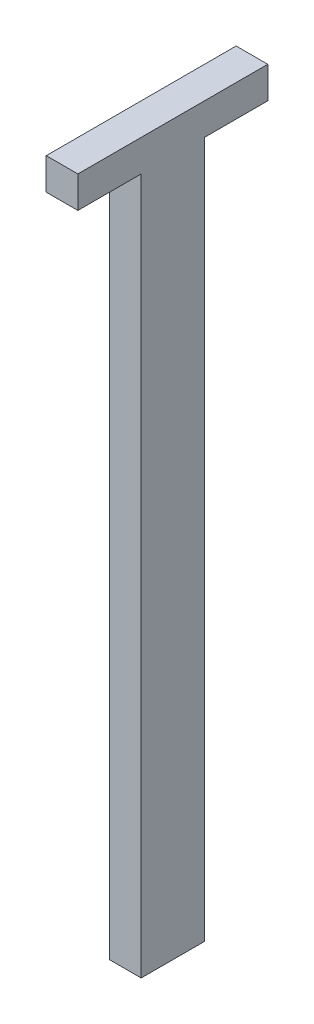
SolidWorks part; units mm, degrees
ref_plane "前视基准面" through (0, 0, 0) normal (0, 0, 1) x (1, 0, 0)
ref_plane "上视基准面" through (0, 0, 0) normal (0, 1, 0) x (1, 0, 0)
ref_plane "右视基准面" through (0, 0, 0) normal (1, 0, 0) x (0, 0, -1)
sketch "草图1" plane through (0, 0, 0) normal (0, 1, 0) x (1, 0, 0)
  line L1 (0, 0) -> (5, 0)
  line L2 (0, 0) -> (0, 10)
  line L3 (0, 10) -> (5, 10)
  line L4 (5, 0) -> (5, 10)
extrude "凸台-拉伸1" add sketch "草图1" along normal blind 110
sketch "草图2" plane through (0, 110, 0) normal (0, 1, 0) x (1, 0, 0)
  line L1 (0, 10) -> (5, 10)
  line L2 (0, 10) -> (0, 0)
  line L3 (0, 0) -> (5, 0)
  line L4 (5, 10) -> (5, 0)
  line L5 (0, 0) -> (5, 0)
  line L6 (0, 0) -> (0, -10)
  line L7 (0, -10) -> (5, -10)
  line L8 (5, 0) -> (5, -10)
  line L9 (0, 10) -> (5, 10)
  line L10 (0, 10) -> (0, 20)
  line L11 (0, 20) -> (5, 20)
  line L12 (5, 10) -> (5, 20)
  line M9 (0, 10) -> (0, 0)
  line M10 (0, 0) -> (5, 0)
  line M11 (5, 0) -> (5, 10)
  line M12 (5, 10) -> (0, 10)
extrude "凸台-拉伸2" add sketch "草图2" along normal blind 5 contours L12 L11 L10 M12 | M12 M9 M10 M11 | L8 L6 L7 M10
